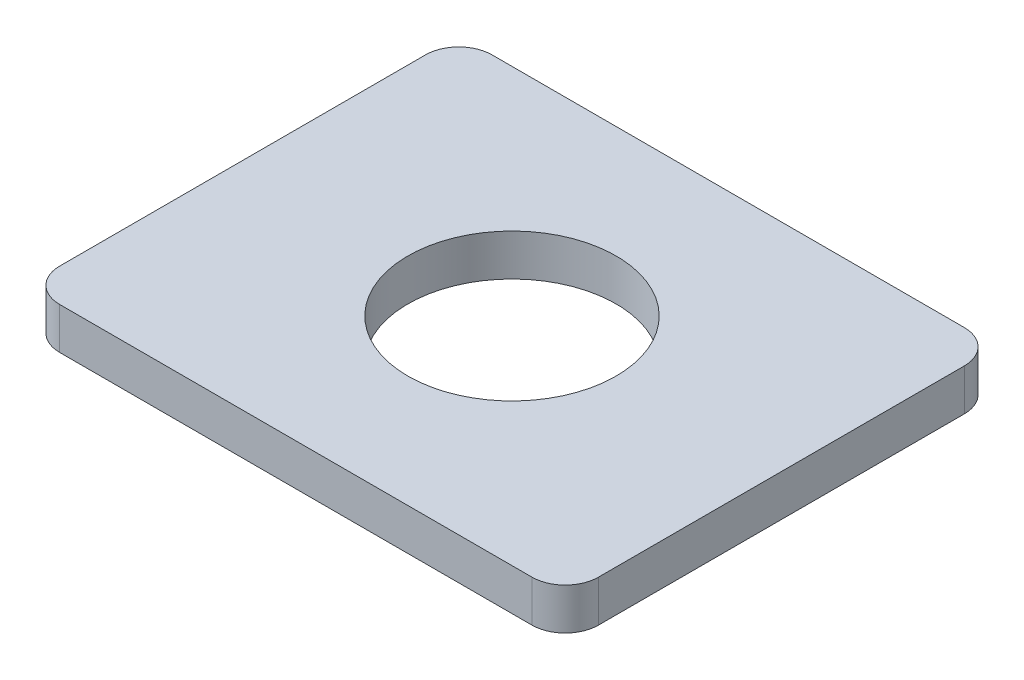
SolidWorks part; units mm, degrees
material "6061 Alloy"
ref_plane "Front" through (0, 0, 0) normal (0, 0, 1) x (1, 0, 0)
ref_plane "Top" through (0, 0, 0) normal (0, 1, 0) x (1, 0, 0)
ref_plane "Right" through (0, 0, 0) normal (1, 0, 0) x (0, 0, -1)
sketch "Sketch1" plane through (0, 0, 0) normal (0, 1, 0) x (1, 0, 0)
  line L1 (18.034, -16.51) -> (-18.034, -16.51)
  line L2 (20.574, -13.97) -> (20.574, 13.97)
  line L3 (18.034, 16.51) -> (-18.034, 16.51)
  line L4 (-20.574, -13.97) -> (-20.574, 13.97)
  line L5 (20.574, -16.51) -> (-20.574, 16.51) construction
  line L6 (20.574, 16.51) -> (-20.574, -16.51) construction
  arc A0 (20.574, 13.97) -> (18.034, 16.51) centre (18.034, 13.97) ccw
  arc A1 (18.034, -16.51) -> (20.574, -13.97) centre (18.034, -13.97) ccw
  arc A2 (-18.034, -16.51) -> (-20.574, -13.97) centre (-18.034, -13.97) cw
  arc A3 (-18.034, 16.51) -> (-20.574, 13.97) centre (-18.034, 13.97) ccw
  point P0 (0, 0)
  dimension "D1" = 2.54
  dimension "D2" = 41.148
  dimension "D3" = 33.02
extrude "Boss-Extrude1" add sketch "Sketch1" along normal blind 3.175
sketch "Sketch2" plane through (0, 3.175, 0) normal (0, 1, 0) x (1, 0, 0)
  circle A0 centre (0, 0) radius 7.9502
  dimension "D1" = 15.9004
extrude "Cut-Extrude1" cut sketch "Sketch2" against normal through all
